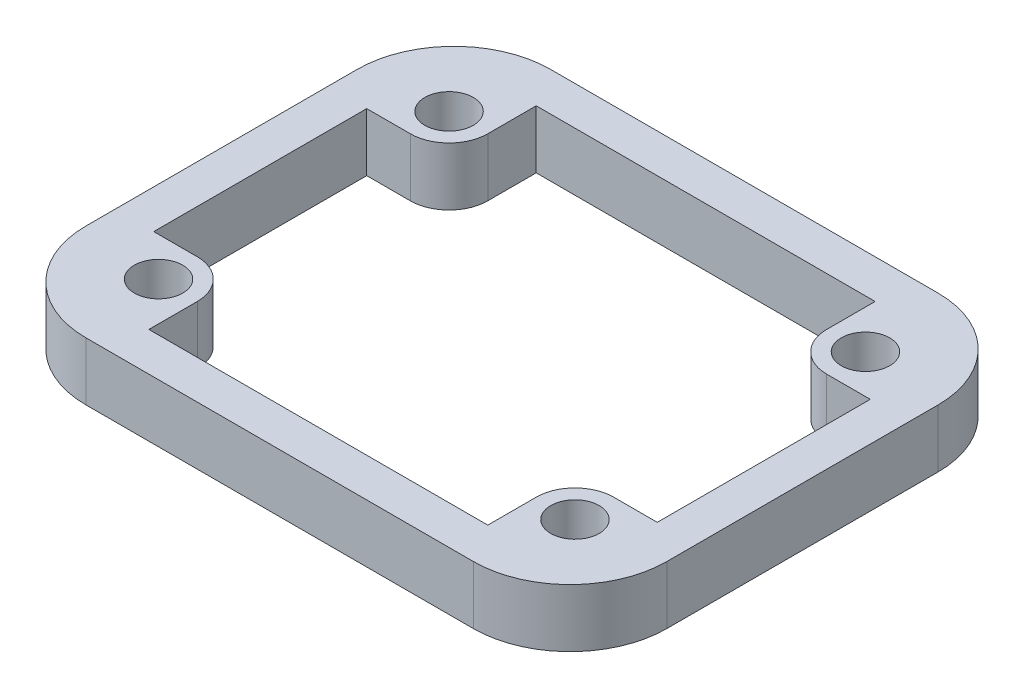
SolidWorks part; units mm, degrees
ref_plane "Front Plane" through (0, 0, 0) normal (0, 0, 1) x (1, 0, 0)
ref_plane "Top Plane" through (0, 0, 0) normal (0, 1, 0) x (1, 0, 0)
ref_plane "Right Plane" through (0, 0, 0) normal (1, 0, 0) x (0, 0, -1)
sketch "Sketch1" plane through (0, 0, 0) normal (0, 1, 0) x (1, 0, 0)
  line L1 (-15, 12) -> (15, 12)
  line L2 (-15, 12) -> (-15, -12)
  line L3 (-15, -12) -> (15, -12)
  line L4 (15, 12) -> (15, -12)
  line L5 (-15, 12) -> (15, -12) construction
  line L6 (-15, -12) -> (15, 12) construction
  point P0 (0, 0)
  dimension "D1" = 30
  dimension "D2" = 24
extrude "Boss-Extrude1" add sketch "Sketch1" along normal blind 3
sketch "Sketch2" plane through (0, 0, 0) normal (0, 1, 0) x (1, 0, 0)
  line L0 (-0.55, 0) -> (0.55, 0) construction
  line L1 (0, -0.55) -> (0, 0.55) construction
  circle A0 centre (-10.75, 7.5) radius 1.25
  circle A4 centre (-10.75, -7.5) radius 1.25
  circle A5 centre (10.75, -7.5) radius 1.25
  circle A6 centre (10.75, 7.5) radius 1.25
  dimension "D1" = 2.5
  dimension "D6" = 7.5
  dimension "D5" = 10.75
extrude "Cut-Extrude1" cut sketch "Sketch2" along normal blind 3
sketch "Sketch4" plane through (0, 0, 0) normal (0, 1, 0) x (1, 0, 0)
  line L0 (0, -1.65) -> (0, 1.65) construction
  line L1 (-1.65, 0) -> (1.65, 0) construction
  line L6 (-10.75, 5.5) -> (-13, 5.5)
  line L7 (-13, 5.5) -> (-13, -5.5)
  line L8 (-13, -5.5) -> (-10.75, -5.5)
  line L9 (-8.75, 7.5) -> (-8.75, 10)
  line L10 (-8.75, 10) -> (8.75, 10)
  line L11 (8.75, 10) -> (8.75, 7.5)
  line L12 (10.75, 5.5) -> (13, 5.5)
  line L13 (13, 5.5) -> (13, -5.5)
  line L14 (13, -5.5) -> (10.75, -5.5)
  line L15 (8.75, -7.5) -> (8.75, -10)
  line L16 (8.75, -10) -> (-8.75, -10)
  line L17 (-8.75, -10) -> (-8.75, -7.5)
  line L18 (-15, 12) -> (-15, -12) construction
  line L19 (15, -12) -> (15, 12) construction
  line L20 (15, 12) -> (-15, 12) construction
  line L21 (-15, -12) -> (15, -12) construction
  arc A0 (-10.75, 5.5) -> (-8.75, 7.5) centre (-10.75, 7.5) ccw
  arc A1 (10.75, 5.5) -> (8.75, 7.5) centre (10.75, 7.5) cw
  arc A2 (10.75, -5.5) -> (8.75, -7.5) centre (10.75, -7.5) ccw
  arc A3 (-10.75, -5.5) -> (-8.75, -7.5) centre (-10.75, -7.5) cw
  dimension "D1" = 4
  dimension "D2" = 2
  dimension "D3" = 2
  dimension "D4" = 2
  dimension "D5" = 2
extrude "Cut-Extrude2" cut sketch "Sketch4" along normal blind 3
fillet "Fillet1" radius 5 4 edges at (-15, 1.5, 12) (15, 1.5, 12) (15, 1.5, -12) (-15, 1.5, -12)
